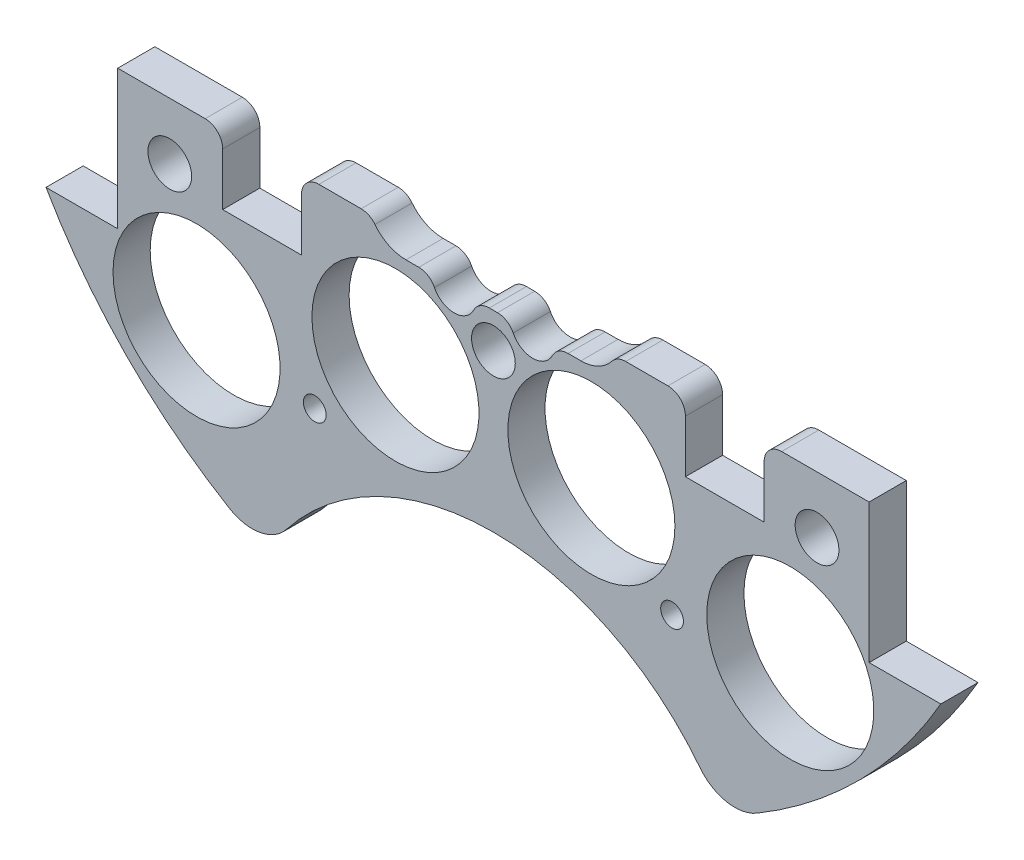
SolidWorks part; units mm, degrees
ref_plane "Front Plane" through (0, 0, 0) normal (0, 0, 1) x (1, 0, 0)
ref_plane "Top Plane" through (0, 0, 0) normal (0, 1, 0) x (1, 0, 0)
ref_plane "Right Plane" through (0, 0, 0) normal (1, 0, 0) x (0, 0, -1)
sketch "Sketch1" plane through (0, 0, 0) normal (0, 0, 1) x (1, 0, 0)
  line L0 (0, 0) -> (-82.1241, 0) construction
  line L1 (0, 0) -> (0, 95.6219) construction
  line L3 (-64.9644, 37.338) -> (-54.5504, 37.338)
  line L5 (-64.9644, -37.338) -> (-54.5504, -37.338)
  line L6 (-54.5504, 37.338) -> (-54.5504, -37.338)
  line L7 (64.9644, -37.338) -> (54.5504, -37.338)
  line L8 (64.9644, 37.338) -> (54.5504, 37.338)
  line L9 (54.5504, 37.338) -> (54.5504, -37.338)
  arc A0 (-64.9644, -37.338) -> (64.9644, -37.338) centre (0, 0) ccw
  circle A1 centre (-46.482, 11.049) radius 1.651
  circle A2 centre (-21.0833, 10.795) radius 1.651
  circle A3 centre (-21.0833, -10.795) radius 1.651
  circle A4 centre (-46.482, -11.049) radius 1.651
  circle A5 centre (46.482, -11.049) radius 1.651
  circle A6 centre (21.0833, -10.795) radius 1.651
  circle A7 centre (21.0833, 10.795) radius 1.651
  circle A8 centre (46.482, 11.049) radius 1.651
  arc A9 (64.9644, 37.338) -> (-64.9644, 37.338) centre (0, 0) ccw
  dimension "D2" = 3.302
  dimension "D3" = 3.302
  dimension "D4" = 25.4
  dimension "D5" = 10.795
  dimension "D10" = 46.482
  dimension "D6" = 74.676
  dimension "D7" = 10.414
  dimension "D8" = 74.93
  dimension "D9" = 74.93
  dimension "D11" = 37.338
extrude "Boss-Extrude2" add sketch "Sketch1" along normal blind 5.3975
sketch "Sketch2" plane through (0, 0, 5.3975) normal (0, 0, 1) x (1, 0, 0)
  line L0 (0, 68.58) -> (0, 55.88) construction
  line L1 (-9.525, 68.58) -> (9.525, 68.58)
  line L2 (-9.525, 68.58) -> (-9.525, 55.88)
  line L3 (-9.525, 55.88) -> (9.525, 55.88)
  line L4 (9.525, 68.58) -> (9.525, 55.88)
  line L5 (-9.525, 62.23) -> (9.525, 62.23) construction
  arc A0 (64.9644, 37.338) -> (-64.9644, 37.338) centre (0, 0) ccw construction
  circle A1 centre (-21.0833, 10.795) radius 1.651 construction
  circle A2 centre (21.0833, 10.795) radius 1.651 construction
  circle A3 centre (-6.731, 62.23) radius 1.143
  circle A4 centre (6.731, 62.23) radius 1.143
  dimension "D4" = 2.286
  dimension "D5" = 0
  dimension "D6" = 6.731
  dimension "D1" = 19.05
  dimension "D2" = 12.7
  dimension "D3" = 55.88
extrude "Cut-Extrude1" cut sketch "Sketch2" against normal through all contours A3 | A4
sketch "Sketch3" plane through (0, 0, 0) normal (0, 0, -1) x (-1, 0, 0)
  line L0 (0, 0) -> (0, -116.2908) construction
  line L1 (0, 0) -> (-153.8039, 0) construction
  line L2 (0, 0) -> (15.2681, -56.9814) construction
  circle A4 centre (-43.1052, -43.1052) radius 12.1285
  circle A6 centre (14.224, -34.29) radius 12.1285
  circle A7 centre (14.224, 34.29) radius 12.1285
  circle A8 centre (-43.1052, 43.1052) radius 12.1285
  circle A11 centre (43.1052, 43.1052) radius 12.1285
  circle A12 centre (-14.224, 34.29) radius 12.1285
  circle A13 centre (-14.224, -34.29) radius 12.1285
  circle A14 centre (43.1052, -43.1052) radius 12.1285
  point P36 (0, 0)
  point P53 (0, 0)
  point P55 (0, 0)
  dimension "D1" = 14.224
  dimension "D2" = 34.29
  dimension "D4" = 15
  dimension "D8" = 24.257
extrude "Cut-Extrude2" cut sketch "Sketch3" against normal through all
sketch "Sketch4" plane through (0, 0, 0) normal (0, 0, -1) x (-1, 0, 0)
  line L1 (-15.7702, 56.3138) -> (12.7925, 56.3138)
  line L2 (-15.7702, 56.3138) -> (-15.7702, 67.9913)
  line L3 (-15.7702, 67.9913) -> (12.7925, 67.9913)
  line L4 (12.7925, 56.3138) -> (12.7925, 67.9913)
extrude "Boss-Extrude3" add sketch "Sketch4" against normal up to surface (5.3975 mm away) up to face at (-55.2337, -43.1052, 5.3975)
sketch "Sketch5" plane through (0, 0, 0) normal (0, 0, -1) x (-1, 0, 0)
  line L1 (-85.044, -17.145) -> (131.6774, -17.145)
  line L2 (-85.044, -17.145) -> (-85.044, 113.4242)
  line L3 (-85.044, 113.4242) -> (131.6774, 113.4242)
  line L4 (131.6774, -17.145) -> (131.6774, 113.4242)
  circle A0 centre (-21.0833, -10.795) radius 1.651 construction
  dimension "D1" = 6.35
extrude "Cut-Extrude4" cut sketch "Sketch5" against normal through all contours L2 L3 L4 L1
sketch "Sketch6" plane through (0, 0, 0) normal (0, 0, -1) x (-1, 0, 0)
  line L0 (-33.02, -67.2621) -> (33.02, -67.2621)
  line L1 (0, 0) -> (0, -146.3858) construction
  arc A0 (-64.9644, -37.338) -> (64.9644, -37.338) centre (0, 0) ccw construction
  circle A1 centre (0, -86.3121) radius 38.1
  dimension "D2" = 76.2
  dimension "D1" = 66.04
  dimension "D3" = 19.05
extrude "Cut-Extrude5" cut sketch "Sketch6" against normal blind 60.96 contours A1
extrude "Cut-Extrude6" cut sketch "Sketch7" against normal through all both and the other way through all
sketch "Sketch7" plane through (-31.3134, 132.614, 31.75) normal (0, 0, 1) x (0, 1, 0)
  line L0 (-132.614, -31.3134) -> (-132.614, 57.8454) construction
  line L1 (-132.614, -31.3134) -> (-222.516, -31.3134) construction
  circle A0 centre (-158.014, 14.4066) radius 3.175
  circle A1 centre (-173.254, -31.3134) radius 3.175
  circle A3 centre (-158.014, -77.0334) radius 3.175
  circle A4 centre (-107.214, -77.0334) radius 3.175
  circle A5 centre (-91.974, -31.3134) radius 3.175
  circle A6 centre (-107.214, 14.4066) radius 3.175
fillet "Fillet1" radius 6.35 1 edges at (-33.001, -67.2714, 2.6987)
fillet "Fillet2" radius 6.35 1 edges at (33.001, -67.2714, 2.6987)
extrude "Cut-Extrude8" cut sketch "Sketch9" against normal blind 29.21
sketch "Sketch9" plane through (-31.3134, 132.559, 28.575) normal (0, 0, 1) x (0, 1, 0)
  line L0 (-132.559, -31.3134) -> (6.1626, -31.3134) construction
  line L2 (-132.559, -31.3134) -> (-132.559, -122.6589) construction
  circle A0 centre (-190.979, 2.9766) radius 1.651
  circle A2 centre (-154.784, -31.3134) radius 1.651
  circle A3 centre (-190.979, -65.6034) radius 1.651
  circle A4 centre (-110.334, -31.3134) radius 1.651
  circle A5 centre (-74.139, -65.6034) radius 1.651
  circle A6 centre (-74.139, 2.9766) radius 1.651
extrude "Cut-Extrude99" cut sketch "Sketch100" against normal blind 29.21
sketch "Sketch100" plane through (-31.3134, 132.559, 22.225) normal (0, 0, 1) x (0, 1, 0)
  line L0 (-143.7712, -34.3645) -> (6.1626, -34.3645) construction
  line L2 (-143.7712, -34.3645) -> (-143.7712, -122.6589) construction
  circle A0 centre (-202.1912, -0.0745) radius 1.651
  circle A2 centre (-165.9962, -34.3645) radius 1.651
  circle A3 centre (-202.1912, -68.6545) radius 1.651
  circle A4 centre (-121.5462, -34.3645) radius 1.651
  circle A5 centre (-85.3512, -68.6545) radius 1.651
  circle A6 centre (-85.3512, -0.0745) radius 1.651
sketch "Sketch102" plane through (0, 0, 0) normal (0, 0, -1) x (-1, 0, 0)
  line L0 (-54.5504, -17.145) -> (54.5504, -17.145) construction
  line L1 (-39.3104, -17.145) -> (-27.8804, -17.145)
  line L2 (-39.3104, -17.145) -> (-39.3104, -27.305)
  line L3 (-39.3104, -27.305) -> (-27.8804, -27.305)
  line L4 (-27.8804, -17.145) -> (-27.8804, -27.305)
  line L5 (0, 15.7454) -> (0, -80.7771) construction
  line L6 (27.8804, -17.145) -> (39.3104, -17.145)
  line L7 (27.8804, -17.145) -> (27.8804, -27.305)
  line L8 (27.8804, -27.305) -> (39.3104, -27.305)
  line L9 (39.3104, -17.145) -> (39.3104, -27.305)
  line L10 (-54.5504, -37.338) -> (-54.5504, -17.145) construction
  dimension "D1" = 11.43
  dimension "D2" = 10.16
  dimension "D3" = 15.24
extrude "Cut-Extrude101" cut sketch "Sketch102" against normal through all
extrude "Cut-Extrude157" cut sketch "Sketch158" against normal blind 97.79
sketch "Sketch158" plane through (30.092, 4.0835, -24.638) normal (0, 0, -1) x (-1, 0, 0)
  line L0 (30.092, -29.4835) -> (30.092, 6.2385) construction
  circle A0 centre (4.1544, -49.7288) radius 1.651
  circle A4 centre (56.0296, -49.7288) radius 1.651
  circle A5 centre (4.1544, 41.3825) radius 1.651
  circle A9 centre (56.0296, 41.3825) radius 1.651
extrude "Cut-Extrude211" cut sketch "Sketch212" against normal blind 48.768 and the other way blind 103.378
sketch "Sketch212" plane through (30.092, 4.0835, 11.4935) normal (0, 0, -1) x (-1, 0, 0)
  line L0 (30.092, -4.0835) -> (148.6336, -4.0835) construction
  line L1 (30.092, -4.0835) -> (30.092, 90.452) construction
  circle A0 centre (-16.898, 21.3165) radius 3.175
  circle A1 centre (77.082, 21.3165) radius 3.175
  circle A2 centre (30.092, 21.3165) radius 3.175
  circle A4 centre (77.082, -29.4835) radius 3.175
  circle A5 centre (30.092, -29.4835) radius 3.175
  circle A6 centre (-16.898, -29.4835) radius 3.175
sketch "Sketch105" plane through (0, 0, 0) normal (0, 0, -1) x (-1, 0, 0)
  line L0 (0, 0) -> (0, -8.89) construction
  line L1 (-12.7, -20.32) -> (-8.89, -20.32)
  line L2 (-12.7, -8.89) -> (12.7, -8.89)
  line L3 (0, -20.32) -> (0, -99.3188) construction
  line L4 (8.89, -20.32) -> (12.7, -20.32)
  line L5 (-2.54, -20.32) -> (2.54, -20.32)
  arc A0 (-12.7, -8.89) -> (-12.7, -20.32) centre (-12.7, -14.605) ccw
  arc A1 (12.7, -8.89) -> (12.7, -20.32) centre (12.7, -14.605) cw
  arc A2 (-8.89, -20.32) -> (-2.54, -20.32) centre (-5.715, -20.32) ccw
  arc A3 (2.54, -20.32) -> (8.89, -20.32) centre (5.715, -20.32) ccw
  dimension "D1" = 11.43
  dimension "D4" = 6.35
  dimension "D5" = 6.35
  dimension "D2" = 12.7
  dimension "D3" = 14.605
  dimension "D6" = 11.43
  dimension "D7" = 5.715
  dimension "D8" = 20.32
extrude "Cut-Extrude104" cut sketch "Sketch105" against normal blind 10
fillet "Fillet3" radius 2.54 10 edges at (-39.3104, -17.145, 2.6987) (-27.8804, -17.145, 2.6987) (-17.8195, -17.145, 2.6987) (-8.89, -20.32, 2.6987) (-2.54, -20.32, 2.6987) (2.54, -20.32, 2.6987) (8.89, -20.32, 2.6987) (17.8195, -17.145, 2.6987) (27.8804, -17.145, 2.6987) (39.3104, -17.145, 2.6987)
